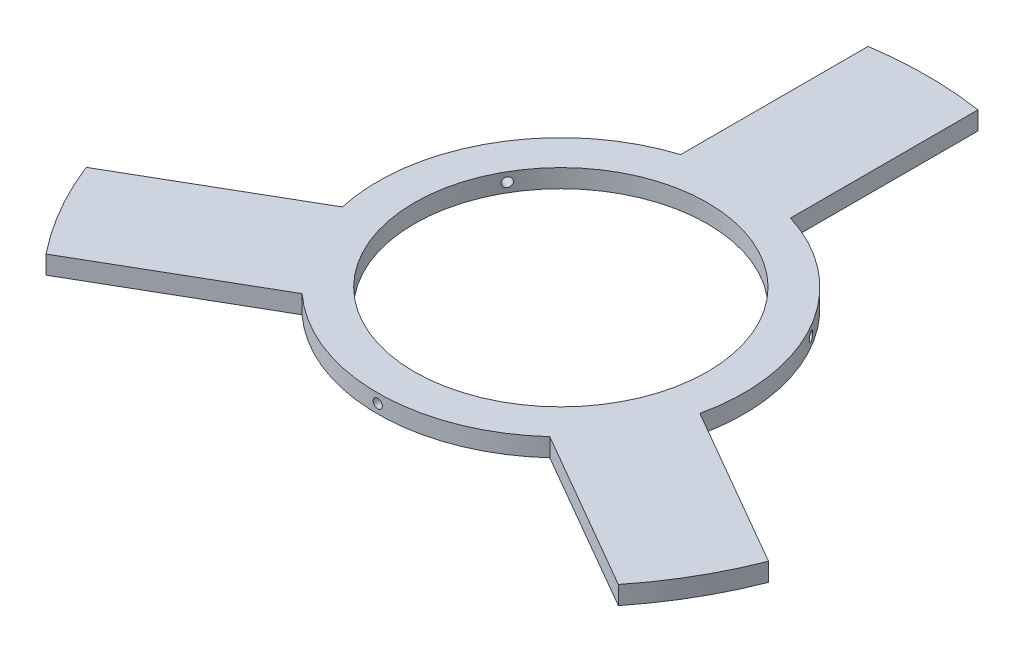
SolidWorks part; units mm, degrees
ref_plane "Front Plane" through (0, 0, 0) normal (0, 0, 1) x (1, 0, 0)
ref_plane "Top Plane" through (0, 0, 0) normal (0, 1, 0) x (1, 0, 0)
ref_plane "Right Plane" through (0, 0, 0) normal (1, 0, 0) x (0, 0, -1)
sketch "Sketch1" plane through (0, 0, 0) normal (0, 1, 0) x (1, 0, 0)
  line L0 (0, 0) -> (0, 127) construction
  line L1 (-19.05, 112.7013) -> (-19.05, 60.5751)
  line L2 (19.05, 112.7013) -> (19.05, 60.5751)
  line L3 (88.0772, -72.8484) -> (42.9346, -46.7854)
  line L4 (107.1272, -39.8529) -> (61.9846, -13.7898)
  line L5 (0, 0) -> (109.9852, -63.5) construction
  line L6 (-107.1272, -39.8529) -> (-61.9846, -13.7898)
  line L7 (-88.0772, -72.8484) -> (-42.9346, -46.7854)
  line L8 (0, 0) -> (-109.9852, -63.5) construction
  line L9 (-19.05, 112.7013) -> (-19.05, 125.5631)
  line L10 (19.05, 112.7013) -> (19.05, 125.5631)
  line L11 (107.1272, -39.8529) -> (118.2659, -46.2838)
  line L12 (88.0772, -72.8484) -> (99.2159, -79.2793)
  line L13 (-107.1272, -39.8529) -> (-118.2659, -46.2838)
  line L14 (-88.0772, -72.8484) -> (-99.2159, -79.2793)
  arc A0 (-118.2659, -46.2838) -> (-99.2159, -79.2793) centre (0, 0) ccw
  circle A1 centre (0, 0) radius 50.8
  arc A2 (19.05, 125.5631) -> (-19.05, 125.5631) centre (0, 0) ccw
  arc A3 (-42.9346, -46.7854) -> (42.9346, -46.7854) centre (0, 0) ccw
  arc A5 (-19.05, 60.5751) -> (-61.9846, -13.7898) centre (0, 0) ccw
  arc A6 (61.9846, -13.7898) -> (19.05, 60.5751) centre (0, 0) ccw
  arc A7 (99.2159, -79.2793) -> (118.2659, -46.2838) centre (0, 0) ccw
  point P23 (0, 0)
  dimension "D1" = 101.6
  dimension "D2" = 254
  dimension "D3" = 127
  dimension "D4" = 12.8618
  dimension "D5" = 19.05
  dimension "D6" = 19.05
  dimension "D7" = 3
extrude "Boss-Extrude1" add sketch "Sketch1" along normal blind 6.35
ref_plane "Plane1" through (0, 0, 63.5) normal (0, 0, 1) x (1, 0, 0)
sketch "Sketch2" plane through (0, 0, 63.5) normal (0, 0, 1) x (1, 0, 0)
  line L0 (0, 6.35) -> (0, 0) construction
  line L1 (42.9346, 6.35) -> (-42.9346, 6.35) construction
  circle A0 centre (0, 3.175) radius 1.5875
  dimension "D1" = 3.175
extrude "Cut-Extrude1" cut sketch "Sketch2" against normal up to surface (12.7248 mm away)
sketch "Sketch4" plane through (0, 0, 0) normal (1, 0, 0) x (0, 0, -1)
  line L0 (0, 12.7) -> (0, -12.7) construction
  dimension "D1" = 25.4
pattern_circular "CirPattern1" count 3 over 360 about axis through (0, 12.7, 0) along (0, -1, 0) of "Cut-Extrude1"
